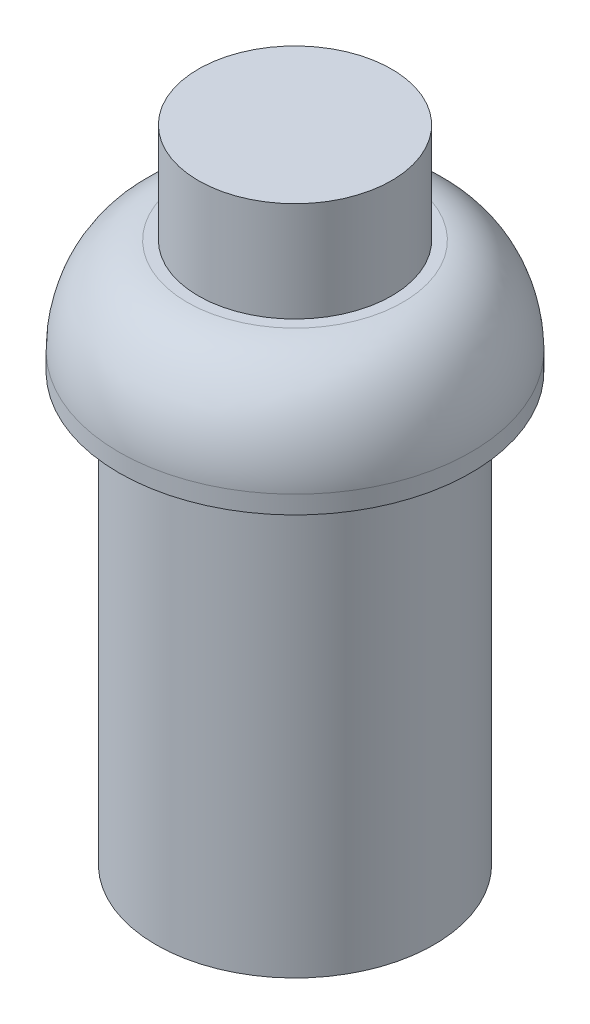
SolidWorks part; units mm, degrees
ref_plane "Front Plane" through (0, 0, 0) normal (0, 0, 1) x (1, 0, 0)
ref_plane "Top Plane" through (0, 0, 0) normal (0, 1, 0) x (1, 0, 0)
ref_plane "Right Plane" through (0, 0, 0) normal (1, 0, 0) x (0, 0, -1)
sketch "Sketch1" plane through (0, 0, 0) normal (0, 1, 0) x (1, 0, 0)
  circle A0 centre (0, 0) radius 3.87
  dimension "D1" = 7.74
extrude "Boss-Extrude1" add sketch "Sketch1" against normal blind 11.89
sketch "Sketch3" plane through (0, 0, 0) normal (0, 0, 1) x (1, 0, 0)
  line L0 (0, 0) -> (0, 3.16)
  line L1 (0, 0) -> (4.9, 0)
  line L2 (0, 3.16) -> (3, 3.16)
  line L3 (4.9, 0) -> (4.9, 0.5)
  spline S0 degree 3 poles (3, 3.16) (4.2836, 3.024) (4.9009, 1.632) (4.9, 0.5) knots 0 0 0 0 1 1 1 1
  dimension "D1" = 3.16
  dimension "D2" = 4.9
  dimension "D3" = 3
  dimension "D4" = 0.5
revolve "Revolve1" add sketch "Sketch3" angle 360 about L0
sketch "Sketch4" plane through (0, 3.16, 0) normal (0, 1, 0) x (1, 0, 0)
  circle A0 centre (0, 0) radius 2.69
  dimension "D1" = 5.38
extrude "Boss-Extrude2" add sketch "Sketch4" along normal blind 2.78
